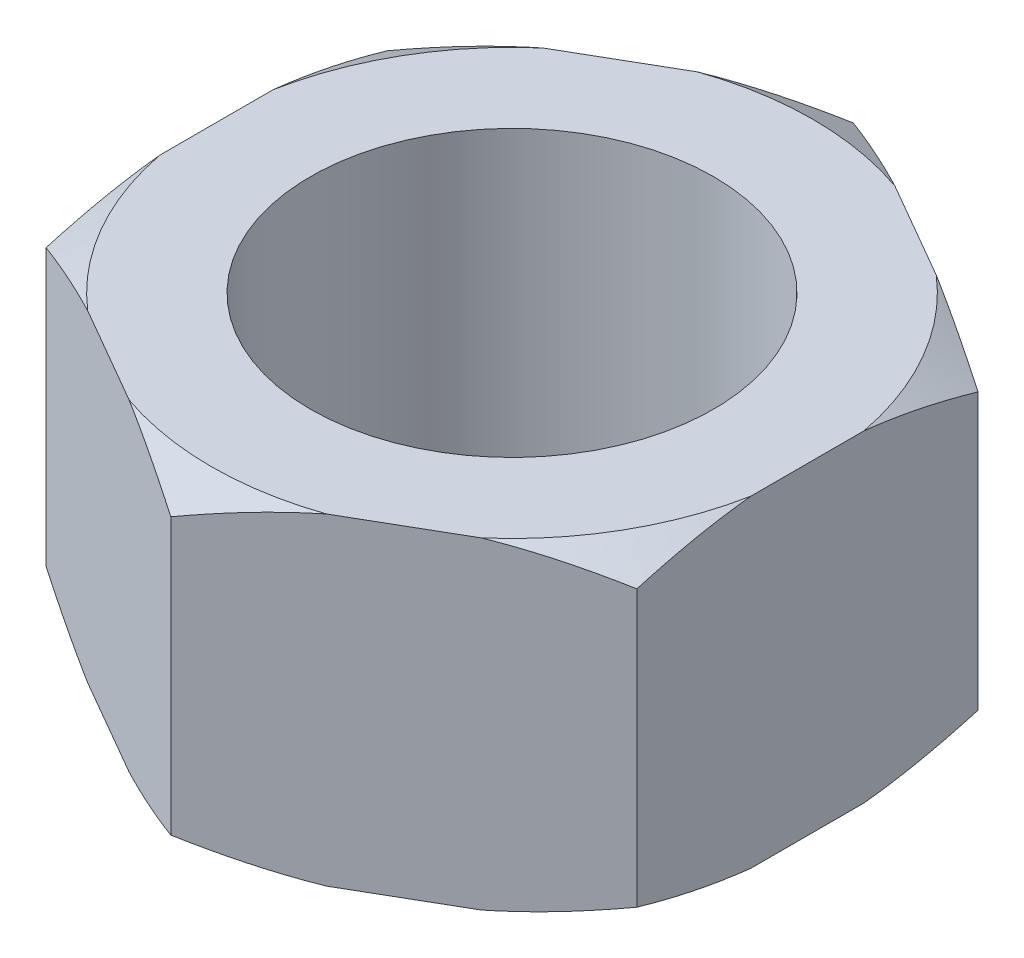
SolidWorks part; units mm, degrees
ref_plane "Front" through (0, 0, 0) normal (0, 0, 1) x (1, 0, 0)
ref_plane "Top" through (0, 0, 0) normal (0, 1, 0) x (1, 0, 0)
ref_plane "Right" through (0, 0, 0) normal (1, 0, 0) x (0, 0, -1)
sketch "Sketch1" plane through (0, 0, 0) normal (0, 1, 0) x (1, 0, 0)
  line L0 (0, 0) -> (0, 20.164) construction
  line L1 (17.4625, 10.082) -> (0, 20.164)
  line L2 (0, 20.164) -> (-17.4625, 10.082)
  line L3 (-17.4625, 10.082) -> (-17.4625, -10.082)
  line L4 (-17.4625, -10.082) -> (0, -20.164)
  line L5 (0, -20.164) -> (17.4625, -10.082)
  line L6 (17.4625, -10.082) -> (17.4625, 10.082)
  circle A0 centre (0, 0) radius 17.4625 construction
  dimension "D1" = 34.925
extrude "Boss-Extrude1" add sketch "Sketch1" along normal mid plane 19.05
sketch "Sketch4" plane through (0, 0, 0) normal (1, 0, 0) x (0, 0, -1)
  line L0 (-10.082, -9.525) -> (10.082, -9.525) construction
  line L1 (-11.9126, -9.525) -> (0, -9.525)
  line L2 (-11.9126, -9.525) -> (-11.9126, 9.525)
  line L3 (-11.9126, 9.525) -> (0, 9.525)
  line L4 (0, -9.525) -> (0, 9.525)
  line L5 (-10.082, 9.525) -> (10.082, 9.525) construction
  line L6 (-17.78, -9.525) -> (-20.164, -8.1486)
  line L7 (-20.164, -9.525) -> (-10.082, -9.525) construction
  line L8 (-20.164, 9.525) -> (-20.164, -9.525) construction
  line L9 (-20.164, -8.1486) -> (-20.164, -9.525)
  line L10 (-20.164, -9.525) -> (-17.78, -9.525)
  line L11 (0, 0) -> (-20.164, 0) construction
  line L12 (-20.164, 9.525) -> (-17.78, 9.525)
  line L13 (-20.164, 8.1486) -> (-20.164, 9.525)
  line L14 (-17.78, 9.525) -> (-20.164, 8.1486)
  dimension "D1" = 11.9126
  dimension "D2" = 30
  dimension "D3" = 17.78
revolve "Cut-Revolve1" cut sketch "Sketch4" angle 360 about L4
thread "Thread1" pitch 2.1167 start angle 0, offset 3.54, length 0, pitch 2.1167, diameter 23.8252
ref_plane "Plane1" through (-11.9126, 13.065, 0) normal (0, 0, 1) x (-1, 0, 0)
sketch "Thread Profile1" plane through (-11.9126, 13.065, 0) normal (0, 0, 1) x (-1, 0, 0)
  line L0 (0, 0) -> (0, 2.1167) construction
  line L1 (0, 0) -> (1.1457, 0.6615)
  line L2 (1.1457, 0.6615) -> (1.1457, 0.926)
  line L3 (1.1457, 0.926) -> (0, 1.5875)
  line L4 (1.1457, 0.7937) -> (0, 0.7937) construction
  line L11 (0, 0) -> (0, 1.5875)
  point P2 (0, 0)
  dimension "Pitch" = 2.1167
  dimension "Profile_Angle" = 60
  dimension "Profile_Land" = 0.2646
  dimension "Profile_Height" = 1.1457
sketch "Sketch9" plane through (0, -9.525, 0) normal (0, -1, 0) x (1, 0, 0)
  circle A0 centre (0, 0) radius 13.335
  circle A1 centre (0, 0) radius 14.605
  dimension "D2" = 26.67
  dimension "D1" = 1.27
extrude "Boss-Extrude2" add sketch "Sketch9" along normal blind 1.27 contours A0
